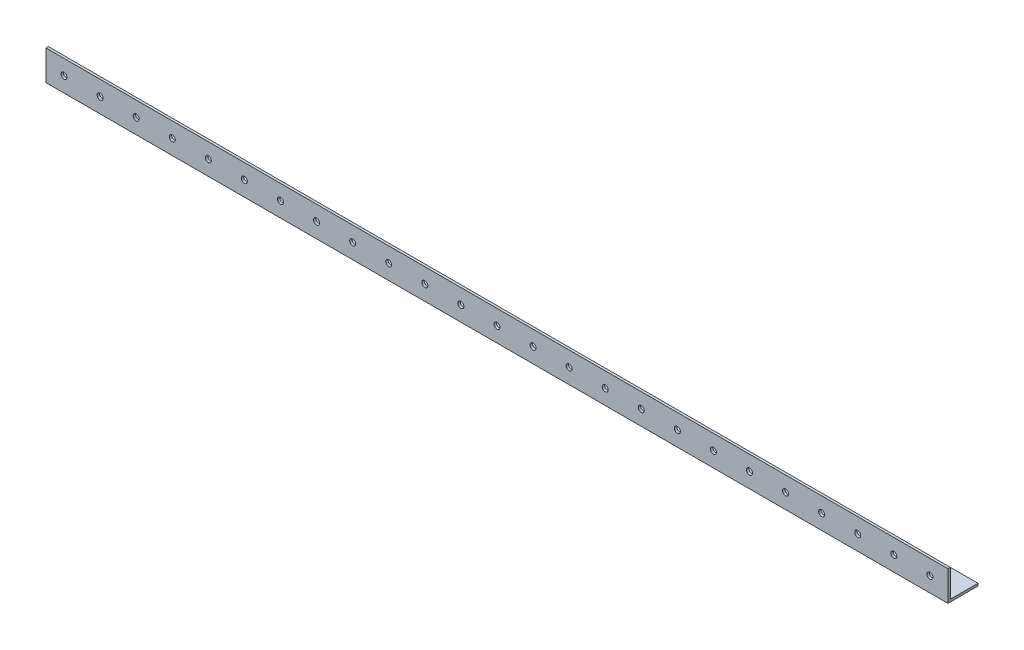
SolidWorks part; units mm, degrees
ref_plane "Спереди" through (0, 0, 0) normal (0, 0, 1) x (1, 0, 0)
ref_plane "Сверху" through (0, 0, 0) normal (0, 1, 0) x (1, 0, 0)
ref_plane "Справа" through (0, 0, 0) normal (1, 0, 0) x (0, 0, -1)
sketch "Эскиз1" plane through (0, 0, 0) normal (1, 0, 0) x (0, 0, -1)
  line L0 (0, 0) -> (0, 50)
  line L1 (0, 0) -> (50, 0)
  dimension "D1" = 50
  dimension "D2" = 50
extrude "Вытянуть-Тонкостенный1" add sketch "Эскиз1" along normal blind 1500 thin
sketch "Эскиз2" plane through (0, 0, 0) normal (0, 0, 1) x (1, 0, 0)
  circle A0 centre (30, 25) radius 5
  circle A1 centre (90, 25) radius 5
  circle A2 centre (150, 25) radius 5
  circle A3 centre (210, 25) radius 5
  circle A8 centre (270, 25) radius 5
  circle A9 centre (330, 25) radius 5
  circle A10 centre (390, 25) radius 5
  circle A11 centre (450, 25) radius 5
  circle A12 centre (510, 25) radius 5
  circle A13 centre (570, 25) radius 5
  circle A14 centre (630, 25) radius 5
  circle A15 centre (690, 25) radius 5
  circle A16 centre (750, 25) radius 5
  circle A17 centre (810, 25) radius 5
  circle A18 centre (870, 25) radius 5
  circle A19 centre (930, 25) radius 5
  circle A20 centre (990, 25) radius 5
  circle A21 centre (1050, 25) radius 5
  circle A22 centre (1110, 25) radius 5
  circle A23 centre (1170, 25) radius 5
  circle A24 centre (1230, 25) radius 5
  circle A25 centre (1290, 25) radius 5
  circle A26 centre (1350, 25) radius 5
  circle A27 centre (1410, 25) radius 5
  circle A28 centre (1470, 25) radius 5
  dimension "D1" = 25
extrude "Вырез-Вытянуть1" cut sketch "Эскиз2" against normal through all
sketch "Эскиз3" plane through (0, 0, 0) normal (0, -1, 0) x (1, 0, 0)
  circle A0 centre (30, -25) radius 5
  circle A1 centre (90, -25) radius 5
  circle A2 centre (150, -25) radius 5
  circle A3 centre (210, -25) radius 5
  circle A4 centre (270, -25) radius 5
  circle A5 centre (330, -25) radius 5
  circle A6 centre (390, -25) radius 5
  circle A7 centre (450, -25) radius 5
  circle A8 centre (510, -25) radius 5
  circle A9 centre (570, -25) radius 5
  circle A10 centre (630, -25) radius 5
  circle A11 centre (690, -25) radius 5
  circle A12 centre (750, -25) radius 5
  circle A13 centre (810, -25) radius 5
  circle A14 centre (870, -25) radius 5
  circle A15 centre (930, -25) radius 5
  circle A16 centre (990, -25) radius 5
  circle A17 centre (1050, -25) radius 5
  circle A18 centre (1110, -25) radius 5
  circle A19 centre (1170, -25) radius 5
  circle A20 centre (1230, -25) radius 5
  circle A21 centre (1290, -25) radius 5
  circle A22 centre (1350, -25) radius 5
  circle A23 centre (1410, -25) radius 5
  circle A24 centre (1470, -25) radius 5
  dimension "D1" = 25
extrude "Вырез-Вытянуть2" cut sketch "Эскиз3" against normal through all
